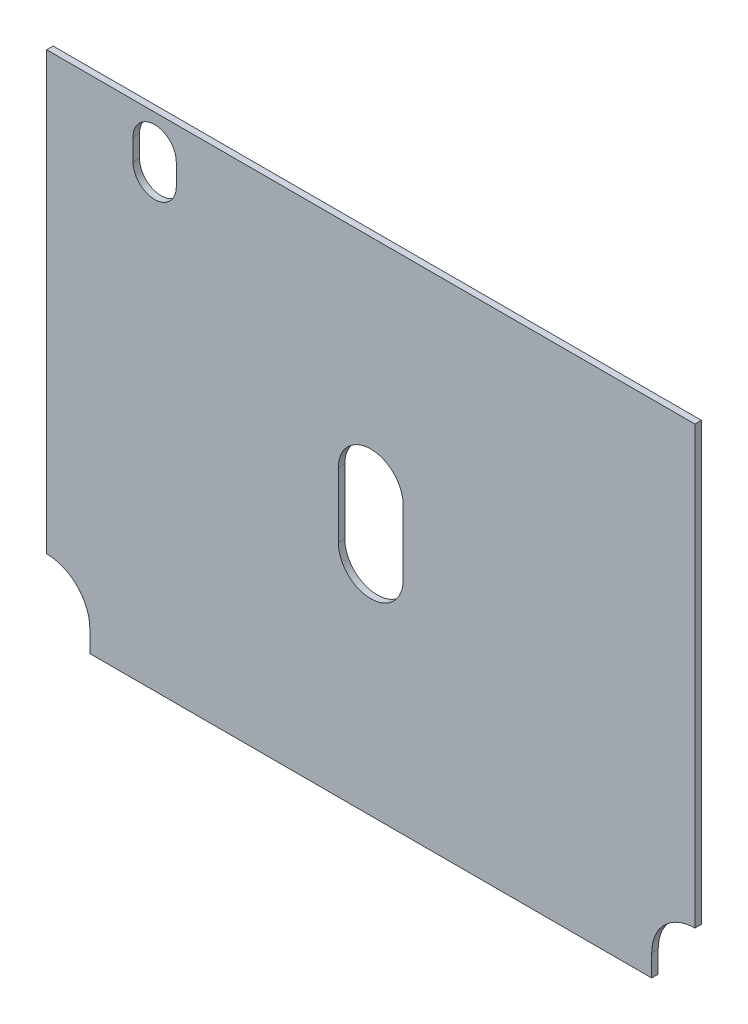
SolidWorks part; units mm, degrees
ref_plane "Face" through (0, 0, 0) normal (0, 0, 1) x (1, 0, 0)
ref_plane "Dessus" through (0, 0, 0) normal (0, 1, 0) x (1, 0, 0)
ref_plane "Droite" through (0, 0, 0) normal (1, 0, 0) x (0, 0, -1)
sketch "Esquisse1" plane through (0, 0, 0) normal (0, 0, 1) x (1, 0, 0)
  line L0 (0, 0) -> (0, 232) construction
  line L1 (150, 232) -> (-150, 232)
  line L2 (-150, 232) -> (-150, 30)
  line L3 (130, 0) -> (-130, 0)
  line L4 (-130, 0) -> (-130, 10)
  line L5 (-150, 30) -> (-150, 0) construction
  line L6 (150, 30) -> (150, 0) construction
  line L7 (130, 0) -> (130, 10)
  line L8 (150, 232) -> (150, 30)
  line L9 (-15, 102) -> (-15, 132)
  line L10 (15, 132) -> (15, 102)
  line L11 (-110, 207) -> (-110, 217)
  line L12 (-90, 217) -> (-90, 207)
  arc A0 (-150, 30) -> (-130, 10) centre (-150, 10) cw
  arc A1 (150, 30) -> (130, 10) centre (150, 10) ccw
  arc A2 (-15, 132) -> (15, 132) centre (0, 132) cw
  arc A3 (-15, 102) -> (15, 102) centre (0, 102) ccw
  arc A4 (-110, 217) -> (-90, 217) centre (-100, 217) cw
  arc A5 (-110, 207) -> (-90, 207) centre (-100, 207) ccw
  dimension "D3" = 20
  dimension "D1" = 232
  dimension "D2" = 150
  dimension "D4" = 30
  dimension "D5" = 30
  dimension "D6" = 30
  dimension "D8" = 100
  dimension "D9" = 20
  dimension "D10" = 10
  dimension "D11" = 15
  dimension "D12" = 50
extrude "Extrusion1" add sketch "Esquisse1" along normal blind 3
